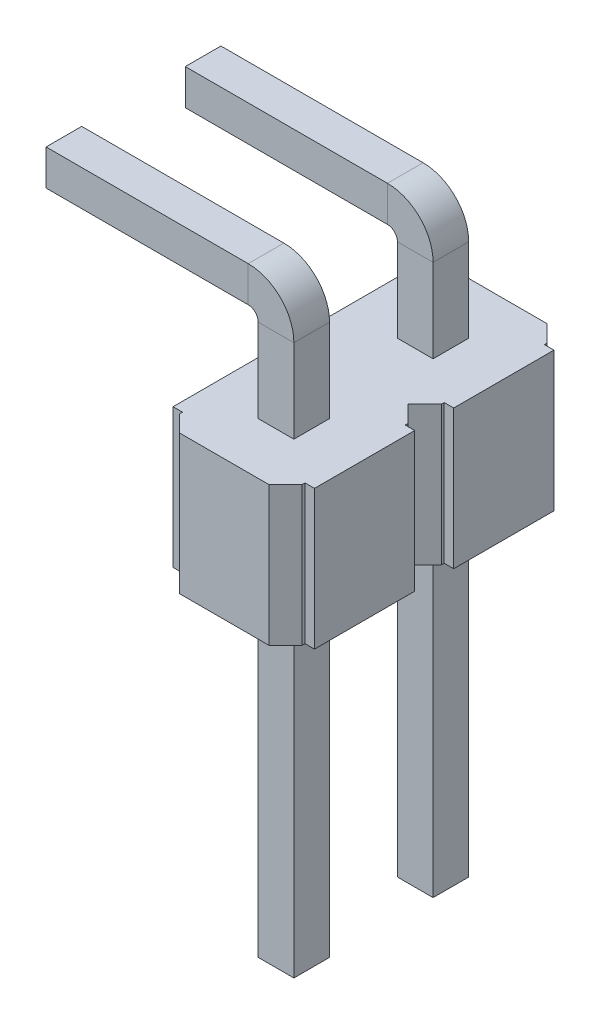
SolidWorks part; units mm, degrees
ref_plane "Front Plane" through (0, 0, 0) normal (0, 0, 1) x (1, 0, 0)
ref_plane "Top Plane" through (0, 0, 0) normal (0, 1, 0) x (1, 0, 0)
ref_plane "Right Plane" through (0, 0, 0) normal (1, 0, 0) x (0, 0, -1)
sketch "Sketch4" plane through (0, 0, 0) normal (0, 1, 0) x (1, 0, 0)
  line L0 (-2.37, -0.9) -> (-2.37, -0.95)
  line L3 (-0.47, 1.25) -> (-2.07, 1.25)
  line L4 (-2.54, 0.9) -> (-2.54, -0.9)
  line L6 (-2.37, 0.9) -> (-2.37, 0.95)
  line L7 (-2.37, 0.9) -> (-2.54, 0.9)
  line L9 (-2.07, 1.25) -> (-2.37, 0.95)
  line L10 (0, -0.9) -> (0, 0.9)
  line L12 (-0.47, 1.25) -> (-0.17, 0.95)
  line L13 (-0.17, 0.9) -> (-0.17, 0.95)
  line L14 (-0.17, 0.9) -> (0, 0.9)
  line L15 (-0.17, -0.9) -> (-0.17, -0.95)
  line L16 (-0.17, -0.9) -> (0, -0.9)
  line L17 (-0.47, -1.25) -> (-0.17, -0.95)
  line L18 (-0.47, -1.25) -> (-2.07, -1.25)
  line L19 (-2.07, -1.25) -> (-2.37, -0.95)
  line L20 (-2.37, -0.9) -> (-2.54, -0.9)
  point P8 (0, 0)
  point P15 (0, 0)
extrude "Boss-Extrude1" add sketch "Sketch4" along normal blind 2.5
sketch "Sketch6" plane through (0, 0, 0) normal (0, -1, 0) x (1, 0, 0)
  line L6 (-1.59, 0.32) -> (-1.59, -0.32)
  line L7 (-1.59, 0.32) -> (-0.95, 0.32)
  line L8 (-1.59, -0.32) -> (-0.95, -0.32)
  line L9 (-0.95, -0.32) -> (-0.95, 0.32)
  line L11 (1.59, 0.32) -> (1.59, -0.32)
  line L12 (1.59, -0.32) -> (0.95, -0.32)
  line L13 (0.95, -0.32) -> (0.95, 0.32)
  line L14 (1.59, 0.32) -> (0.95, 0.32)
  point P15 (-1.27, 0)
  point P18 (-1.27, 0.32)
extrude "Cut-Extrude1" cut sketch "Sketch6" against normal blind 2.5
ref_plane "Plane3" through (0, -6, 0) normal (0, 1, 0) x (1, 0, 0)
sketch "Sketch15" plane through (0, -6, 0) normal (0, 1, 0) x (1, 0, 0)
  line L0 (-1.59, 0.32) -> (-0.95, 0.32) construction
  line L1 (-0.95, 0.32) -> (-0.95, -0.32) construction
  line L2 (-0.95, -0.32) -> (-1.59, -0.32) construction
  line L3 (-1.59, -0.32) -> (-1.59, 0.32) construction
  line L4 (-1.59, 0.32) -> (-0.95, 0.32)
  line L5 (-0.95, 0.32) -> (-0.95, -0.32)
  line L6 (-0.95, -0.32) -> (-1.59, -0.32)
  line L7 (-1.59, -0.32) -> (-1.59, 0.32)
  line L8 (-1.59, 0) -> (-0.95, 0) construction
  line L9 (-0.95, 0) -> (-1.27, 0) construction
ref_plane "Plane4" through (0, 0, 0) normal (0, 0, -1) x (1, 0, 0)
sketch "Sketch17" plane through (0, 0, 0) normal (0, 0, -1) x (1, 0, 0)
  line L0 (-1.27, 6) -> (-1.27, -4)
  line L1 (-0.95, 6) -> (-1.59, 6) construction
  line L2 (-1.77, -4.5) -> (-5.52, -4.5)
  arc A0 (-1.77, -4.5) -> (-1.27, -4) centre (-1.77, -4) ccw
  point P7 (-1.27, -4.5)
  dimension "D3" = 0.5
  dimension "D1" = 10.5
  dimension "D2" = 4.25
sweep "Sweep1" add profiles "Sketch15" path "Sketch17"
chamfer "Chamfer4" distance 0.12 angle 45 8 edges at (-5.52, 4.5, -0.32) (-5.52, 4.82, 0) (-5.52, 4.5, 0.32) (-5.52, 4.18, 0) (-1.27, -6, 0.32) (-0.95, -6, 0) (-1.27, -6, -0.32) (-1.59, -6, 0)
pattern_linear "LPattern5" count 2 spacing 2.5 along (0, 0, 1) of "Boss-Extrude1", "Sweep1", "Chamfer4"
